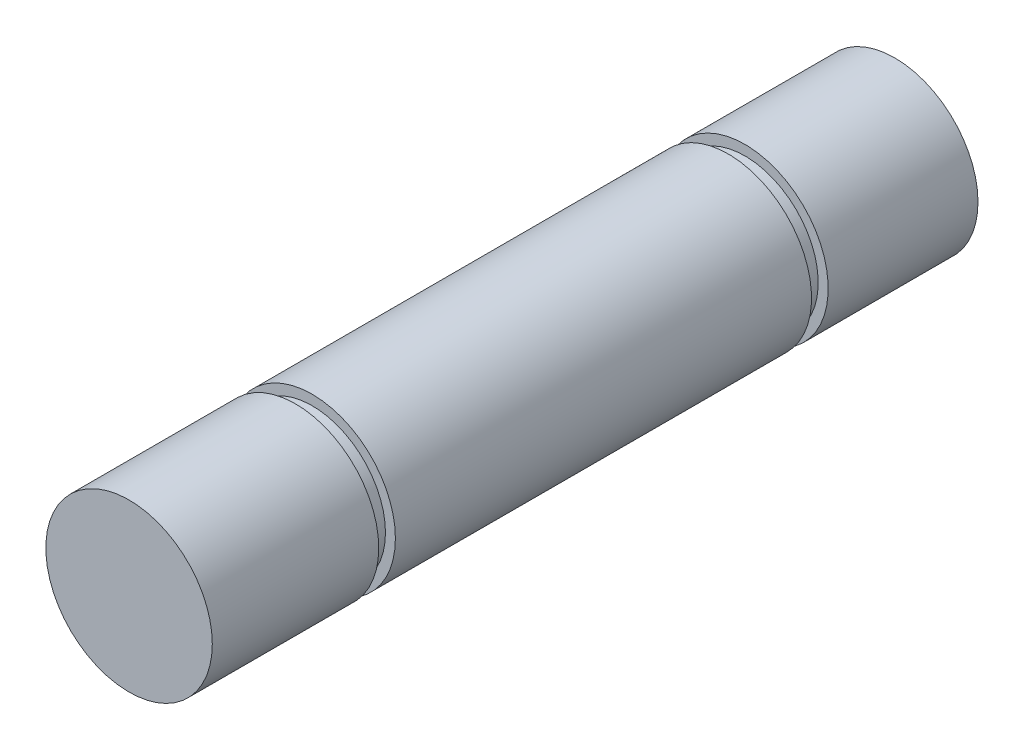
SolidWorks part; units mm, degrees
ref_plane "Płaszczyzna przednia" through (0, 0, 0) normal (0, 0, 1) x (1, 0, 0)
ref_plane "Płaszczyzna górna" through (0, 0, 0) normal (0, 1, 0) x (1, 0, 0)
ref_plane "Płaszczyzna prawa" through (0, 0, 0) normal (1, 0, 0) x (0, 0, -1)
sketch "Sketch1" plane through (0, 0, 0) normal (0, 0, 1) x (1, 0, 0)
  circle A0 centre (0, 0) radius 2.5
  dimension "D1" = 5
extrude "Boss-Extrude1" add sketch "Sketch1" along normal blind 23
sketch "Szkic1" plane through (0, 0, 23) normal (0, 0, 1) x (1, 0, 0)
  circle A0 centre (0, 0) radius 2.2014
  circle A1 centre (0, 0) radius 2.5
  dimension "D1" = 4.4027
  dimension "D2" = 5
extrude "Wytnij-wyciągnięcie1" cut sketch "Szkic1" against normal blind 0.5 from offset 5 offset against normal yes
sketch "Szkic2" plane through (0, 0, 0) normal (0, 0, -1) x (-1, 0, 0)
  circle A0 centre (0, 0) radius 2.5
  circle A1 centre (0, 0) radius 2.2
  dimension "D1" = 4.4
  dimension "D2" = 5
extrude "Wytnij-wyciągnięcie2" cut sketch "Szkic2" along normal blind 0.5 from offset 5 offset against normal yes
